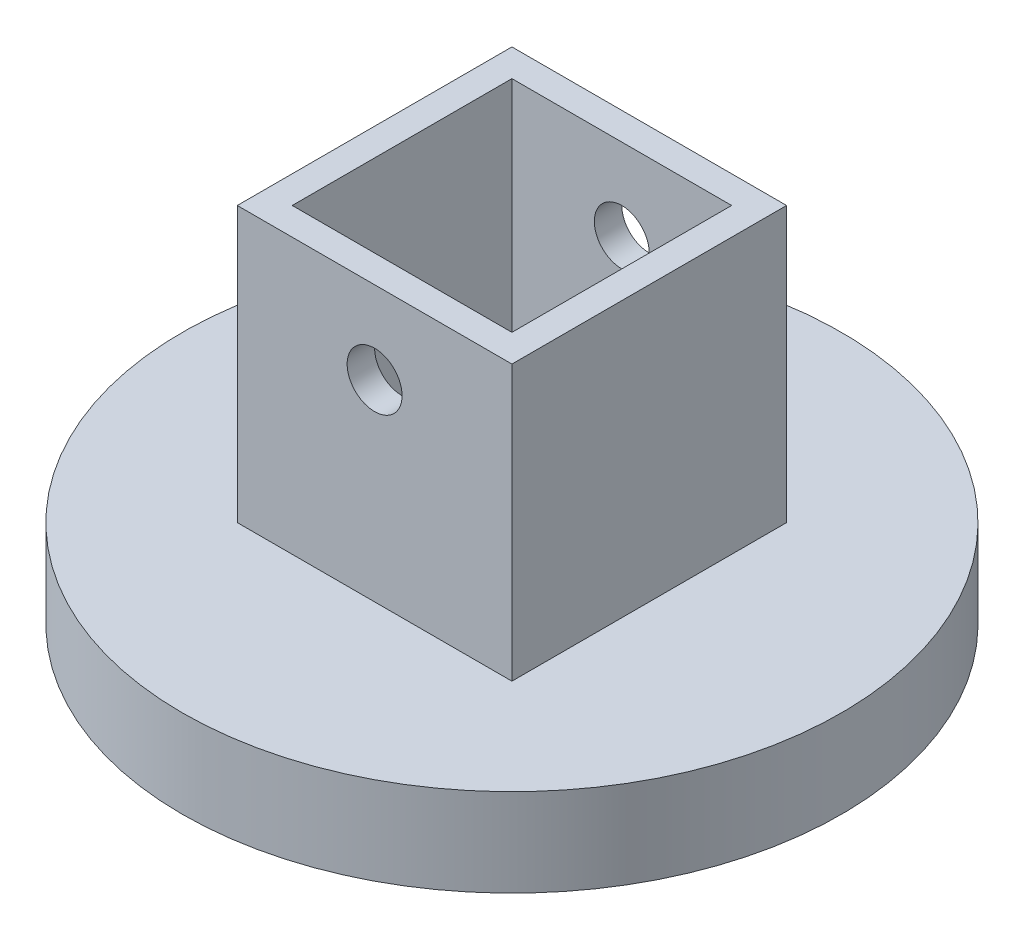
SolidWorks part; units mm, degrees
material "Polyetheretherketone (PEEK)"
ref_plane "Front Plane" through (0, 0, 0) normal (0, 0, 1) x (1, 0, 0)
ref_plane "Top Plane" through (0, 0, 0) normal (0, 1, 0) x (1, 0, 0)
ref_plane "Right Plane" through (0, 0, 0) normal (1, 0, 0) x (0, 0, -1)
sketch "Sketch1" plane through (0, 0, 0) normal (0, 1, 0) x (1, 0, 0)
  circle A0 centre (0, 0) radius 38.1
  dimension "OuterDiameter" = 76.2
extrude "Boss-Extrude1" add sketch "Sketch1" along normal blind 10.16
sketch "Sketch2" plane through (0, 10.16, 0) normal (0, 1, 0) x (1, 0, 0)
  line L1 (15.875, -15.875) -> (-15.875, -15.875)
  line L2 (15.875, -15.875) -> (15.875, 15.875)
  line L3 (15.875, 15.875) -> (-15.875, 15.875)
  line L4 (-15.875, -15.875) -> (-15.875, 15.875)
  line L5 (15.875, -15.875) -> (-15.875, 15.875) construction
  line L6 (15.875, 15.875) -> (-15.875, -15.875) construction
  point P0 (0, 0)
  dimension "OutsideWall" = 31.75
extrude "Boss-Extrude3" add sketch "Sketch2" along normal blind 31.75
sketch "Sketch3" plane through (0, 41.91, 0) normal (0, 1, 0) x (1, 0, 0)
  line L1 (-12.7, 12.7) -> (12.7, 12.7)
  line L2 (-12.7, 12.7) -> (-12.7, -12.7)
  line L3 (-12.7, -12.7) -> (12.7, -12.7)
  line L4 (12.7, 12.7) -> (12.7, -12.7)
  line L5 (-12.7, 12.7) -> (12.7, -12.7) construction
  line L6 (-12.7, -12.7) -> (12.7, 12.7) construction
  point P0 (0, 0)
  dimension "InsideHole" = 25.4
extrude "Cut-Extrude1" cut sketch "Sketch3" against normal through all
sketch "Sketch4" plane through (0, 0, 15.875) normal (0, 0, 1) x (1, 0, 0)
  line L0 (-15.875, 10.16) -> (15.875, 10.16) construction
  circle A0 centre (0, 32.385) radius 3.175
  point P6 (0, 10.16)
  dimension "BoltHole" = 6.35
  dimension "D1" = 22.225
extrude "Cut-Extrude2" cut sketch "Sketch4" against normal through all
equation "\"ScopeLengthUnit\"= 10 * \"ScaleFactor\""
equation "\"EyepieceRadius\"= 0.75 * \"ScaleFactor\""
equation "\"ScopeThickness\"= 0.1 * \"ScaleFactor\""
equation "\"ScopeLensWidth\"= 2 * \"ScaleFactor\""
equation "\"ScopeOutsideRadius\"= 2.1 * \"ScaleFactor\""
equation "\"PegWidth\"=1"
equation "\"SupportOutsideDiam\"= \"ScopeOutsideRadius\" * 2 + .25"
equation "\"RotatingDiskDiam\"=3"
equation "\"LegSeatWidth\"=4 "
equation "\"BoltCircleDiam\"= ( \"RotatingDiskDiam\" + \"RotatingDiskHousingDiameter\" ) / 2"
equation "\"RotatingDiskHousingDiameter\"= (\"RotatingDiskDiam\" + 2)"
equation "\"OuterDiameter@Sketch1\"=\"RotatingDiskDiam\""
equation "\"InsideHole@Sketch3\"=\"PegWidth\""
equation "\"OutsideWall@Sketch2\"=\"PegWidth\"+.25"
equation "\"LegSeatHeight\"=2"
equation "\"LegThickness\"=0.25"
equation "\"LegHeight\"=48"
equation "\"LegBoltDiam\"=0.25"
equation "\"PinHeight\"=\"RotDiskLidHeight\" + \"RotDiskHeight\" + \"PinBoltDiam\"*3"
equation "\"PinBoltDiam\"=0.25"
equation "\"BoltHole@Sketch4\"=\"PinBoltDiam\""
equation "\"RotDiskHeight\"=0.5"
equation "\"D1@Boss-Extrude1\"= \"RotDiskHeight\" - .1"
equation "\"RotDiskLidHeight\"= 0.5"
equation "\"D1@Sketch4\"=\"RotDiskLidHeight\"+\"PinBoltDiam\"*1.5"
equation "\"D1@Boss-Extrude3\"=\"RotDiskLidHeight\"+\"PinBoltDiam\"*3"
equation "\"DiskSeatPinDiam\"=0.25"
equation "\"ScaleFactor\"= 1"
